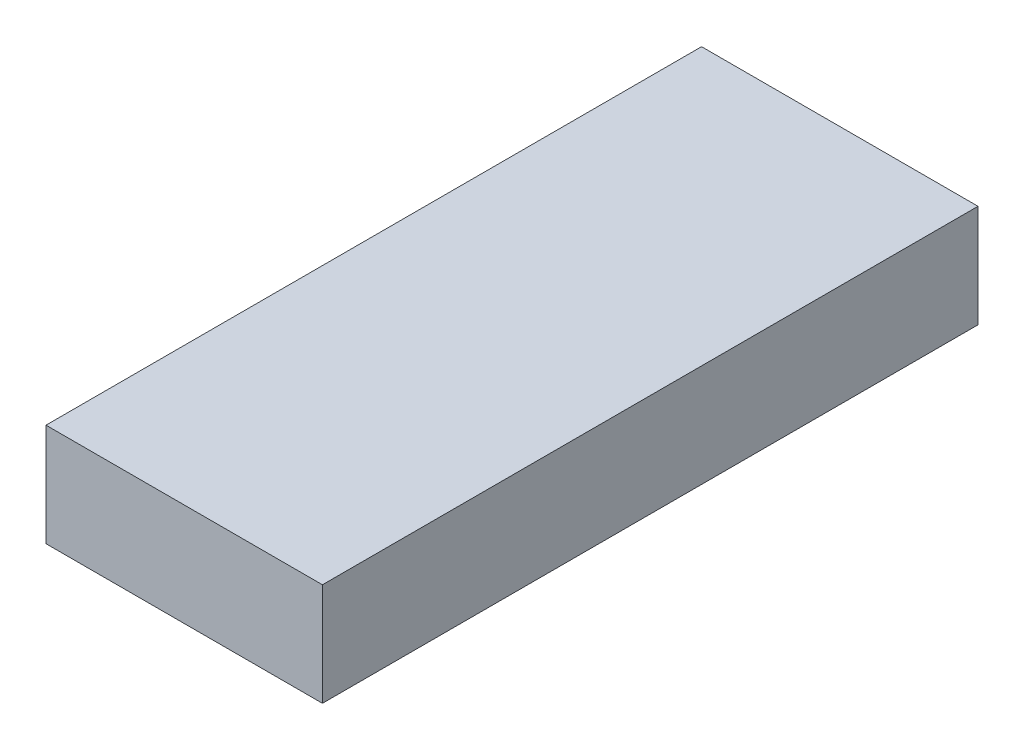
SolidWorks part; units mm, degrees
ref_plane "正面" through (0, 0, 0) normal (0, 0, 1) x (1, 0, 0)
ref_plane "平面" through (0, 0, 0) normal (0, 1, 0) x (1, 0, 0)
ref_plane "右側面" through (0, 0, 0) normal (1, 0, 0) x (0, 0, -1)
sketch "ｽｹｯﾁ1" plane through (0, 0, 0) normal (0, 0, 1) x (1, 0, 0)
  line L1 (-11.896, 4.0035) -> (23.104, 4.0035)
  line L2 (-11.896, 4.0035) -> (-11.896, -8.9965)
  line L3 (-11.896, -8.9965) -> (23.104, -8.9965)
  line L4 (23.104, 4.0035) -> (23.104, -8.9965)
  dimension "D1" = 35
  dimension "D2" = 13
extrude "ﾎﾞｽ - 押し出し1" add sketch "ｽｹｯﾁ1" along normal blind 83
